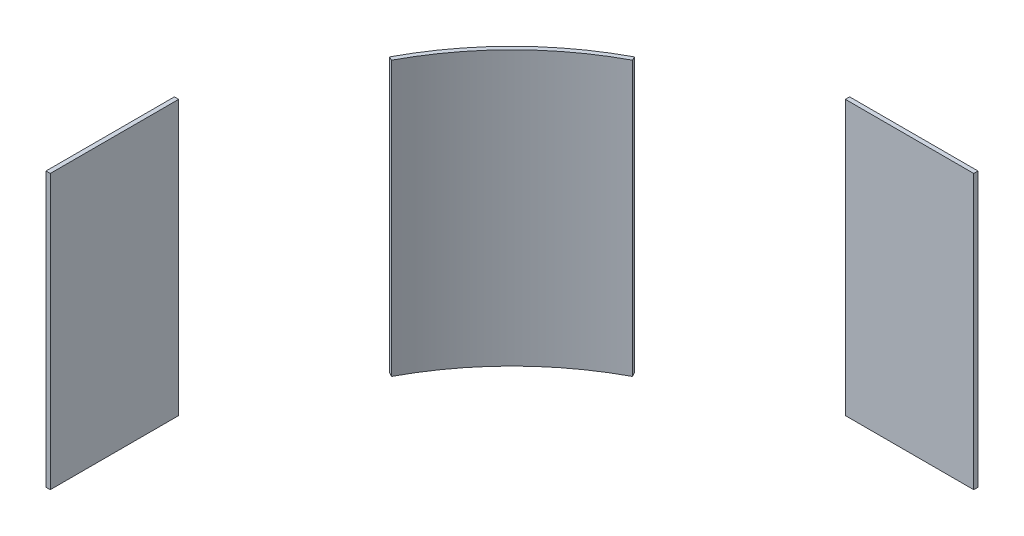
SolidWorks part; units mm, degrees
ref_plane "Front Plane" through (0, 0, 0) normal (0, 0, 1) x (1, 0, 0)
ref_plane "Top Plane" through (0, 0, 0) normal (0, 1, 0) x (1, 0, 0)
ref_plane "Right Plane" through (0, 0, 0) normal (1, 0, 0) x (0, 0, -1)
sketch "Sketch1" plane through (0, 0, 0) normal (0, 1, 0) x (1, 0, 0)
  line L0 (0, 17) -> (0.22, 17) construction
  line L1 (0.22, 17) -> (0.22, 19.25) construction
  line L2 (0.22, 19.25) -> (7.72, 19.25) construction
  line L3 (-17, 0) -> (-17, -0.22) construction
  line L4 (-17, -0.22) -> (-19.25, -0.22) construction
  line L5 (-19.25, -0.22) -> (-19.25, -7.72) construction
  line L6 (-19.25, -0.22) -> (-19.5, -0.22)
  line L7 (-19.5, -0.22) -> (-19.5, -7.72)
  line L8 (-19.5, -7.72) -> (-19.25, -7.72)
  line L9 (-19.25, -7.72) -> (-19.25, -0.22)
  line L10 (0.22, 19.25) -> (0.22, 19.5)
  line L11 (0.22, 19.5) -> (7.72, 19.5)
  line L12 (7.72, 19.5) -> (7.72, 19.25)
  line L13 (7.72, 19.25) -> (0.22, 19.25)
  line L14 (-7.974, 15.0138) -> (-0.1904, 19.1478) construction
  line L15 (-15.0138, 7.974) -> (-19.1478, 0.1904) construction
  line L16 (-8.0913, 15.2346) -> (-7.974, 15.0138)
  line L17 (-15.2346, 8.0913) -> (-15.0138, 7.974)
  circle A0 centre (0, 0) radius 17 construction
  arc A1 (-15.0138, 7.974) -> (-7.974, 15.0138) centre (0, 0) cw
  arc A2 (-19.1478, 0.1904) -> (-19.25, -0.22) centre (-18.375, -0.22) ccw construction
  arc A3 (-0.1904, 19.1478) -> (0.22, 19.25) centre (0.22, 18.375) cw construction
  arc A4 (-15.2346, 8.0913) -> (-8.0913, 15.2346) centre (0, 0) cw
  dimension "D1" = 34
  dimension "D8" = 18.375
  dimension "D2" = 17.22
  dimension "D3" = 17.22
  dimension "D4" = 7.5
  dimension "D5" = 7.5
  dimension "D6" = 2.25
  dimension "D7" = 2.25
  dimension "D9" = 0.25
  dimension "D10" = 0.25
  dimension "D11" = 18.375
  dimension "D12" = 0.25
extrude "Extrude1" add sketch "Sketch1" along normal mid plane 16
